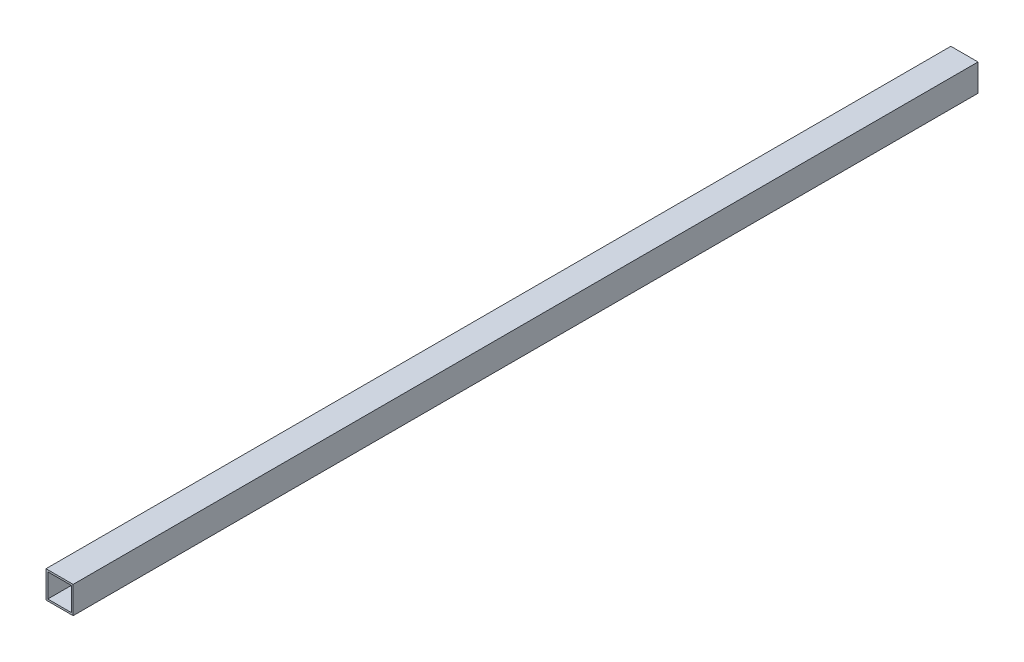
SolidWorks part; units mm, degrees
ref_plane "Front Plane" through (0, 0, 0) normal (0, 0, 1) x (1, 0, 0)
ref_plane "Top Plane" through (0, 0, 0) normal (0, 1, 0) x (1, 0, 0)
ref_plane "Right Plane" through (0, 0, 0) normal (1, 0, 0) x (0, 0, -1)
curve "Curve1"
  spline degree 1 poles (0, 0, 0) (0, 0, 2000) knots 0 0 1 1
sketch "Sketch1" plane through (0, 0, 0) normal (0, 0, 1) x (1, 0, 0)
  line L0 (0, 35.3535) -> (0, -33.8384) construction
  line L1 (-30, 30) -> (30, 30)
  line L2 (-30, 30) -> (-30, -30)
  line L3 (-30, -30) -> (30, -30)
  line L4 (30, 30) -> (30, -30)
  line L5 (-26, 26) -> (26, 26)
  line L6 (-26, 26) -> (-26, -26)
  line L7 (-26, -26) -> (26, -26)
  line L8 (26, 26) -> (26, -26)
  line L9 (-39.3939, 0) -> (41.5152, 0) construction
  dimension "D1" = 60
  dimension "D2" = 52
sweep "Sweep1" add profiles "Sketch1" path "Curve1"
